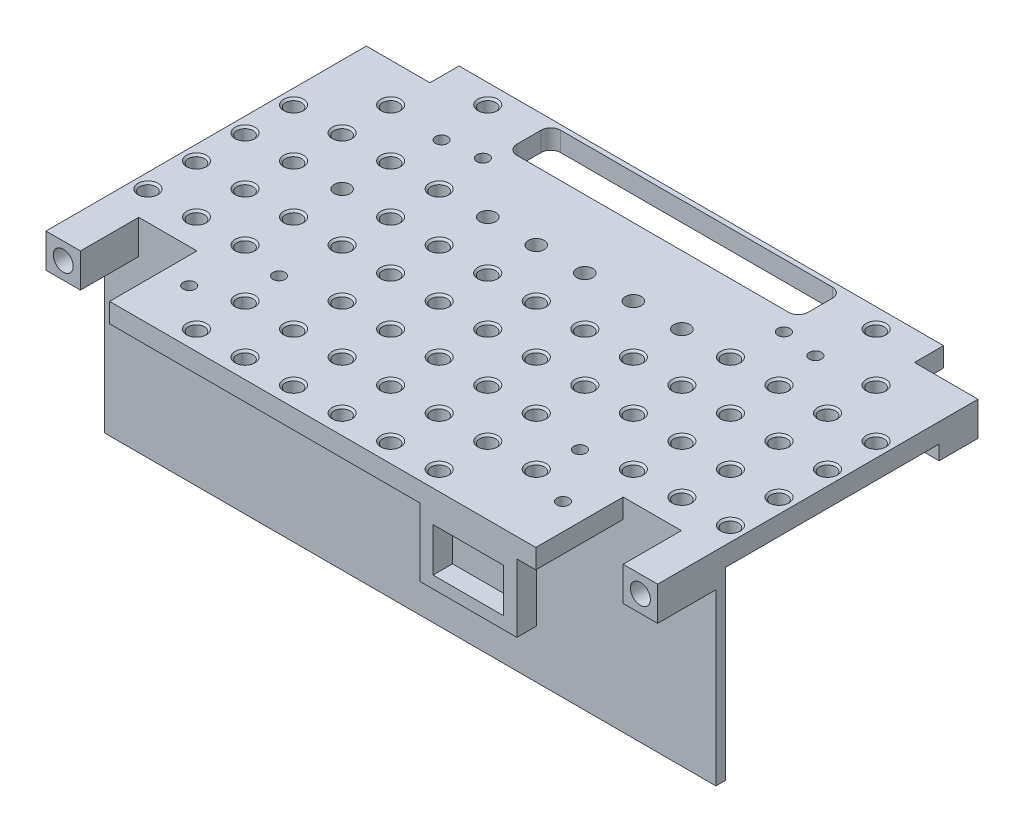
SolidWorks part; units mm, degrees
ref_plane "Front Plane" through (0, 0, 0) normal (0, 0, 1) x (1, 0, 0)
ref_plane "Top Plane" through (0, 0, 0) normal (0, 1, 0) x (1, 0, 0)
ref_plane "Right Plane" through (0, 0, 0) normal (1, 0, 0) x (0, 0, -1)
sketch "Sketch1" plane through (0, 0, 0) normal (0, 1, 0) x (1, 0, 0)
  line L0 (-63, 0) -> (63, 0) construction
  line L1 (-63, -33) -> (-55.9, -33)
  line L2 (-63, -33) -> (-63, 33)
  line L3 (-63, 33) -> (-55.9, 33)
  line L4 (63, -33) -> (63, 33)
  line L5 (-63, -33) -> (63, 33) construction
  line L6 (-63, 33) -> (63, -33) construction
  line L8 (-55.9, 33) -> (-55.9, 40)
  line L9 (-55.9, 40) -> (55.9, 40)
  line L10 (55.9, 33) -> (55.9, 40)
  line L11 (55.9, 33) -> (63, 33)
  line L12 (55.9, -33) -> (55.9, -40)
  line L13 (-55.9, -40) -> (55.9, -40)
  line L14 (-55.9, -33) -> (-55.9, -40)
  line L15 (55.9, -33) -> (63, -33)
  point P0 (0, 0)
  point P10 (0, 40)
  dimension "D1" = 126
  dimension "D2" = 66
  dimension "D3" = 7.1
  dimension "D4" = 7
extrude "Boss-Extrude1" add sketch "Sketch1" along normal blind 4
sketch "Sketch3" plane through (0, 0, 0) normal (0, -1, 0) x (1, 0, 0)
  line L0 (-63, -33) -> (-63, 33) construction
  line L1 (-55.9, -33) -> (-63, -33)
  line L2 (-55.9, -33) -> (-55.9, -25)
  line L3 (-55.9, -25) -> (-63, -25)
  line L4 (-63, -33) -> (-63, -25)
  dimension "D1" = 8
extrude "Boss-Extrude3" add sketch "Sketch3" along normal blind 3
sketch "Sketch4" plane through (0, 0, -33) normal (0, 0, -1) x (-1, 0, 0)
  line L0 (63, -3) -> (55.9, 4) construction
  circle A0 centre (59.45, 0.5) radius 2.05
  dimension "D1" = 4.1
extrude "Cut-Extrude1" cut sketch "Sketch4" against normal blind 7
mirror "Mirror1" about plane through (0, 0, 0) normal (1, 0, 0) of "Cut-Extrude1", "Boss-Extrude3"
mirror "Mirror2" about plane through (0, 0, 0) normal (0, 0, 1) of "Cut-Extrude1", "Boss-Extrude3", "Mirror1"
sketch "Sketch5" plane through (0, 4, 0) normal (0, 1, 0) x (1, 0, 0)
  line L0 (55.9, 40) -> (-55.9, 40) construction
  line L1 (-30, 38) -> (30, 38)
  line L2 (-30, 38) -> (-30, 29)
  line L3 (-30, 29) -> (30, 29)
  line L4 (30, 38) -> (30, 29)
  point P4 (0, 29)
  dimension "D1" = 2
  dimension "D2" = 9
  dimension "D3" = 60
extrude "Cut-Extrude2" cut sketch "Sketch5" against normal through all
sketch "Sketch6" plane through (0, 4, 0) normal (0, 1, 0) x (1, 0, 0)
  line L1 (-38.5, -28) -> (38.5, -28) construction
  line L2 (-38.5, -28) -> (-38.5, 24) construction
  line L3 (-38.5, 24) -> (38.5, 24) construction
  line L4 (38.5, -28) -> (38.5, 24) construction
  line L5 (-38.5, -28) -> (38.5, 24) construction
  line L6 (-38.5, 24) -> (38.5, -28) construction
  circle A0 centre (-38.5, 24) radius 1.25
  circle A1 centre (38.5, 24) radius 1.25
  circle A2 centre (38.5, -28) radius 1.25
  circle A3 centre (-38.5, -28) radius 1.25
  point P0 (0, -2)
  point P9 (0, -2)
  dimension "D4" = 2.5
  dimension "D1" = 77
  dimension "D2" = 52
  dimension "D3" = 2
fillet "Fillet1" radius 2 4 edges at (-30, 2, -38) (-30, 2, -29) (30, 2, -38) (30, 2, -29)
sketch "Sketch7" plane through (0, 4, 0) normal (0, 1, 0) x (1, 0, 0)
  line L0 (55.9, 33) -> (55.9, 40) construction
  line L1 (-55.9, 40) -> (55.9, 40)
  line L2 (-55.9, 40) -> (-55.9, 39)
  line L3 (-55.9, 39) -> (55.9, 39)
  line L4 (55.9, 40) -> (55.9, 39)
  line L5 (-55.9, -33) -> (-55.9, -40) construction
  line L6 (55.9, -40) -> (-55.9, -40)
  line L7 (55.9, -40) -> (55.9, -39)
  line L8 (55.9, -39) -> (-55.9, -39)
  line L9 (-55.9, -40) -> (-55.9, -39)
  dimension "D1" = 1
  dimension "D2" = 1
extrude "Cut-Extrude3" cut sketch "Sketch7" against normal through all
sketch "Sketch8" plane through (0, 0, 0) normal (0, -1, 0) x (1, 0, 0)
  line L0 (63, 25) -> (63, -25) construction
  line L1 (63, 21) -> (-63, 21)
  line L2 (63, 21) -> (63, 19)
  line L3 (63, 19) -> (-63, 19)
  line L4 (-63, 21) -> (-63, 19)
  line L5 (-63, -25) -> (-63, 25) construction
  line L7 (55.9, 39) -> (-55.9, 39) construction
  dimension "D1" = 20
  dimension "D2" = 2
extrude "Boss-Extrude4" add sketch "Sketch8" along normal blind 38
sketch "Sketch9" plane through (0, 4, 0) normal (0, 1, 0) x (1, 0, 0)
  line L0 (63, -21) -> (-63, -21) construction
  line L1 (-55.9, -39) -> (-43.9, -39)
  line L2 (-55.9, -39) -> (-55.9, -21)
  line L3 (-55.9, -21) -> (-43.9, -21)
  line L4 (-43.9, -39) -> (-43.9, -21)
  dimension "D1" = 12
extrude "Cut-Extrude4" cut sketch "Sketch9" against normal blind 10
sketch "Sketch10" plane through (0, -3, 0) normal (0, -1, 0) x (1, 0, 0)
  line L1 (-63, 25) -> (-55.9, 25)
  line L2 (-63, 25) -> (-63, 21)
  line L3 (-63, 21) -> (-55.9, 21)
  line L4 (-55.9, 25) -> (-55.9, 21)
  line L5 (55.9, 25) -> (63, 25)
  line L6 (55.9, 25) -> (55.9, 21)
  line L7 (55.9, 21) -> (63, 21)
  line L8 (63, 25) -> (63, 21)
extrude "Boss-Extrude5" add sketch "Sketch10" against normal up to surface (3 mm away) up to face at (29.4143, 0, 29)
ref_plane "Plane2" through (-56, 0, 0) normal (-1, 0, 0) x (0, 0, 1)
sketch "Sketch12" plane through (-56, 0, 0) normal (-1, 0, 0) x (0, 0, 1)
  line L0 (21, -5.8) -> (21, -16.2)
  line L1 (21, -38) -> (21, -3) construction
  line L2 (21, -16.2) -> (23.7, -13.5)
  line L3 (23.7, -13.5) -> (23.7, -8.5)
  line L4 (23.7, -8.5) -> (21, -5.8)
  line L5 (23.7, -11) -> (21, -11) construction
  line L6 (21, -3) -> (33, -3) construction
  line L7 (23.1, -9) -> (21.6, -9)
  line L8 (23.1, -9) -> (23.1, -13)
  line L9 (23.1, -13) -> (21.6, -13)
  line L10 (21.6, -9) -> (21.6, -13)
  line L11 (21, -20.8) -> (21, -31.2)
  line L12 (21, -31.2) -> (23.7, -28.5)
  line L13 (23.7, -28.5) -> (23.7, -23.5)
  line L14 (23.7, -23.5) -> (21, -20.8)
  line L15 (23.1, -24) -> (21.6, -24)
  line L16 (23.1, -24) -> (23.1, -28)
  line L17 (23.1, -28) -> (21.6, -28)
  line L18 (21.6, -24) -> (21.6, -28)
  line L19 (23.7, -26) -> (21, -26) construction
  point P13 (22.35, -11)
  point P14 (23.1, -11)
  dimension "D1" = 1.5
  dimension "D2" = 0.6
  dimension "D3" = 0.6
  dimension "D4" = 4
  dimension "D5" = 45
  dimension "D6" = 5
  dimension "D7" = 8
  dimension "D8" = 2
extrude "Boss-Extrude6" add sketch "Sketch12" against normal blind 2
ref_plane "Plane3" through (-49.9, 0, 0) normal (1, 0, 0) x (0, 0, -1)
mirror "Mirror3" about plane through (-49.9, 0, 0) normal (1, 0, 0) of "Boss-Extrude6"
sketch "Sketch13" plane through (0, 0, 0) normal (0, -1, 0) x (1, 0, 0)
  line L0 (-28, -29) -> (28, -29) construction
  line L1 (-20, -19.5) -> (20, -19.5)
  line L2 (-20, -19.5) -> (-20, -21.5)
  line L3 (-20, -21.5) -> (20, -21.5)
  line L4 (20, -19.5) -> (20, -21.5)
  point P4 (0, -21.5)
  dimension "D1" = 40
  dimension "D2" = 2
  dimension "D3" = 7.5
extrude "Boss-Extrude7" add sketch "Sketch13" along normal up to surface (38 mm away) up to face at (0, -38, 20)
sketch "Sketch14" plane through (0, 0, 0) normal (1, 0, 0) x (0, 0, -1)
  line L0 (-19, -19) -> (19.5, -19) construction
  line L1 (-19, -38) -> (-19, 0) construction
  line L2 (19.5, -38) -> (19.5, 0) construction
  line L3 (0.25, -38) -> (0.25, 0) construction
  line L4 (-19, 0) -> (25, 0) construction
  line L5 (-21, -31.2) -> (-23.7, -28.5) construction
  line L6 (-23.1, -24) -> (-21.6, -24) construction
  line L7 (-23.1, -28) -> (-23.1, -24) construction
  line L8 (-21.6, -28) -> (-23.1, -28) construction
  line L9 (-21.6, -24) -> (-21.6, -28) construction
  line L10 (-21, -20.8) -> (-21, -31.2) construction
  line L11 (-23.7, -23.5) -> (-21, -20.8) construction
  line L12 (-23.7, -28.5) -> (-23.7, -23.5) construction
  line L13 (-23.1, -13) -> (-23.1, -9) construction
  line L14 (-23.1, -9) -> (-21.6, -9) construction
  line L15 (-21.6, -9) -> (-21.6, -13) construction
  line L16 (-21.6, -13) -> (-23.1, -13) construction
  line L17 (-21, -5.8) -> (-21, -16.2) construction
  line L18 (-21, -16.2) -> (-23.7, -13.5) construction
  line L19 (-23.7, -13.5) -> (-23.7, -8.5) construction
  line L20 (-23.7, -8.5) -> (-21, -5.8) construction
  line L21 (-21, -31.2) -> (-23.7, -28.5) construction
  line L22 (-23.1, -24) -> (-21.6, -24) construction
  line L23 (-23.1, -28) -> (-23.1, -24) construction
  line L24 (-21.6, -28) -> (-23.1, -28) construction
  line L25 (-21.6, -24) -> (-21.6, -28) construction
  line L26 (-21, -20.8) -> (-21, -31.2) construction
  line L27 (-23.7, -23.5) -> (-21, -20.8) construction
  line L28 (-23.7, -28.5) -> (-23.7, -23.5) construction
  line L29 (-23.1, -13) -> (-23.1, -9) construction
  line L30 (-23.1, -9) -> (-21.6, -9) construction
  line L31 (-21.6, -9) -> (-21.6, -13) construction
  line L32 (-21.6, -13) -> (-23.1, -13) construction
  line L33 (-21, -5.8) -> (-21, -16.2) construction
  line L34 (-21, -16.2) -> (-23.7, -13.5) construction
  line L35 (-23.7, -13.5) -> (-23.7, -8.5) construction
  line L36 (-23.7, -8.5) -> (-21, -5.8) construction
  line L37 (24.2, -8.5) -> (21.5, -5.8)
  line L38 (24.2, -13.5) -> (24.2, -8.5)
  line L39 (21.5, -16.2) -> (24.2, -13.5)
  line L40 (21.5, -5.8) -> (21.5, -16.2)
  line L41 (22.1, -13) -> (23.6, -13)
  line L42 (22.1, -9) -> (22.1, -13)
  line L43 (23.6, -9) -> (22.1, -9)
  line L44 (23.6, -13) -> (23.6, -9)
  line L45 (24.2, -28.5) -> (24.2, -23.5)
  line L46 (24.2, -23.5) -> (21.5, -20.8)
  line L47 (21.5, -20.8) -> (21.5, -31.2)
  line L48 (22.1, -24) -> (22.1, -28)
  line L49 (22.1, -28) -> (23.6, -28)
  line L50 (23.6, -28) -> (23.6, -24)
  line L51 (23.6, -24) -> (22.1, -24)
  line L52 (21.5, -31.2) -> (24.2, -28.5)
  point P11 (0.25, -19)
extrude "Boss-Extrude8" add sketch "Sketch14" along normal mid plane 2
sketch "Sketch15" plane through (0, 0, 0) normal (1, 0, 0) x (0, 0, -1)
  line L0 (19.5, 0) -> (19.5, -5)
  line L1 (19.5, -38) -> (19.5, 0) construction
  line L2 (19.5, -5) -> (16.6132, 0)
  line L3 (-19, 0) -> (25, 0) construction
  line L4 (16.6132, 0) -> (19.5, 0)
  dimension "D1" = 60
  dimension "D2" = 5
extrude "Boss-Extrude9" add sketch "Sketch15" against normal up to surface and the other way up to surface up to face at (-20, -19, -20.5) other way up to face at (20, -19, -20.5)
sketch "Sketch16" plane through (0, 0, 39) normal (0, 0, 1) x (1, 0, 0)
  line L0 (40, 0) -> (20, -14) construction
  line L1 (40, 0) -> (20, 0)
  line L2 (40, 0) -> (40, -14)
  line L3 (40, -14) -> (20, -14)
  line L4 (20, 0) -> (20, -14)
  line L5 (55.9, 0) -> (-43.9, 0) construction
  line L6 (22.75, -2.5) -> (37.25, -2.5)
  line L7 (22.75, -2.5) -> (22.75, -11.5)
  line L8 (22.75, -11.5) -> (37.25, -11.5)
  line L9 (37.25, -2.5) -> (37.25, -11.5)
  line L10 (22.75, -2.5) -> (37.25, -11.5) construction
  line L11 (22.75, -11.5) -> (37.25, -2.5) construction
  line L12 (63, -38) -> (63, -3) construction
  point P5 (30, -7)
  dimension "D1" = 20
  dimension "D2" = 14
  dimension "D3" = 14.5
  dimension "D4" = 9
  dimension "D5" = 23
extrude "Boss-Extrude10" add sketch "Sketch16" against normal blind 4
sketch "Sketch17" plane through (0, 0, 0) normal (0, -1, 0) x (1, 0, 0)
  line L6 (-43.9, 21) -> (-55.9, 21) construction
  line L7 (55.9, 39) -> (43.9, 39)
  line L8 (55.9, 39) -> (55.9, 21)
  line L9 (55.9, 21) -> (43.9, 21)
  line L10 (43.9, 39) -> (43.9, 21)
  line L13 (-43.9, 39) -> (-43.9, 21) construction
extrude "Cut-Extrude5" cut sketch "Sketch17" against normal through all
sketch "Sketch18" plane through (0, 4, 0) normal (0, 1, 0) x (1, 0, 0)
  line L5 (-55.9, 39) -> (55.9, 39) construction
  line L6 (55.9, 33) -> (49.9, 33)
  line L7 (55.9, 33) -> (55.9, 39)
  line L8 (55.9, 39) -> (49.9, 39)
  line L9 (49.9, 33) -> (49.9, 39)
  line L11 (-55.9, 33) -> (-49.9, 33)
  line L12 (-55.9, 33) -> (-55.9, 39)
  line L13 (-55.9, 39) -> (-49.9, 39)
  line L14 (-49.9, 33) -> (-49.9, 39)
extrude "Cut-Extrude6" cut sketch "Sketch18" against normal through all
sketch "Sketch20" plane through (0, 4, 0) normal (0, 1, 0) x (1, 0, 0)
  line L0 (-31, 25) -> (31, -17) construction
  line L1 (-31, 25) -> (31, 25) construction
  line L2 (-31, 25) -> (-31, -17) construction
  line L3 (-31, -17) -> (31, -17) construction
  line L4 (31, 25) -> (31, -17) construction
  line L5 (-38.5, 26) -> (38.5, 26) construction
  line L6 (-38.5, 26) -> (-38.5, -26) construction
  line L7 (-38.5, -26) -> (38.5, -26) construction
  line L8 (38.5, 26) -> (38.5, -26) construction
  line L11 (38.5, 26) -> (-38.5, -26) construction
  circle A0 centre (-31, 25) radius 3 construction
  circle A1 centre (-31, -17) radius 3 construction
  circle A2 centre (31, -17) radius 3 construction
  circle A3 centre (31, 25) radius 3 construction
  circle A4 centre (-38.5, 26) radius 3 construction
  circle A5 centre (38.5, 26) radius 3 construction
  circle A6 centre (38.5, -26) radius 3 construction
  circle A7 centre (-38.5, -26) radius 3 construction
  point P18 (0, 4)
  dimension "D3" = 6
  dimension "D1" = 42
  dimension "D2" = 62
  dimension "D4" = 4
  dimension "D6" = 77
  dimension "D7" = 52
sketch "Sketch22" plane through (0, 4, 0) normal (0, 1, 0) x (1, 0, 0)
  circle A0 centre (-31, 25) radius 1.25
  circle A1 centre (31, 25) radius 1.25
  circle A2 centre (31, -17) radius 1.25
  circle A3 centre (-31, -17) radius 1.25
  dimension "D1" = 2.5
extrude "Cut-Extrude7" cut sketch "Sketch22" against normal up to surface (4 mm away) up to face at (15, 0, 33.5)
sketch "Sketch23" plane through (0, 4, 0) normal (0, 1, 0) x (1, 0, 0)
  line L0 (-63, 0) -> (63, 0) construction
  line L1 (63, -33) -> (63, 33) construction
  line L2 (0, -39) -> (0, 39) construction
  line L3 (-49.9, 39) -> (49.9, 39) construction
  line L4 (-63, -5) -> (63, -5) construction
  line L5 (-63, -15) -> (63, -15) construction
  line L9 (-10, -5) -> (-10, -15) construction
  line L10 (-20, -5) -> (-20, -15) construction
  line L11 (-30, -5) -> (-30, -15) construction
  line L12 (-40, -5) -> (-40, -15) construction
  line L13 (-50, -5) -> (-50, -15) construction
  line L14 (-60, -5) -> (-60, -15) construction
  circle A0 centre (0, -5) radius 1.65
  circle A1 centre (0, -15) radius 1.65
  circle A2 centre (-10, -5) radius 1.65
  circle A3 centre (-20, -5) radius 1.65
  circle A4 centre (-30, -5) radius 1.65
  circle A5 centre (-40, -5) radius 1.65
  circle A6 centre (-50, -5) radius 1.65
  circle A7 centre (-60, -5) radius 1.65
  circle A8 centre (-60, -15) radius 1.65
  circle A9 centre (-50, -15) radius 1.65
  circle A10 centre (-40, -15) radius 1.65
  circle A11 centre (-20, -15) radius 1.65
  circle A12 centre (-10, -15) radius 1.65
  point P6 (0, 0)
  point P11 (0, 0)
  point P18 (0, -5)
  point P21 (0, -15)
  dimension "D1" = 3.3
  dimension "D4" = 10
  dimension "D2" = 5
  dimension "D3" = 10
  dimension "D5" = 10
  dimension "D6" = 10
  dimension "D7" = 10
  dimension "D8" = 10
  dimension "D9" = 10
extrude "Cut-Extrude8" cut sketch "Sketch23" against normal through all
mirror "Mirror4" about plane through (0, 0, 0) normal (0, 0, 1) of "Cut-Extrude8"
mirror "Mirror5" about plane through (0, 0, 0) normal (1, 0, 0) of "Mirror4", "Cut-Extrude8"
sketch "Sketch24" plane through (0, 4, 0) normal (0, 1, 0) x (1, 0, 0)
  line L0 (-40, 15) -> (-20, 15) construction
  line L1 (20, 15) -> (40, 15) construction
  line L2 (-40, 15) -> (-40, 39) construction
  line L3 (-49.9, 39) -> (49.9, 39) construction
  line L4 (-50, 15) -> (-50, 33) construction
  line L5 (-49.9, 33) -> (-63, 33) construction
  line L6 (-50, 25) -> (-40, 25) construction
  line L7 (-50, 35) -> (-40, 35) construction
  line L8 (40, 15) -> (40, 39) construction
  line L9 (50, 15) -> (50, 33) construction
  line L10 (63, 33) -> (49.9, 33) construction
  line L11 (40, 25) -> (50, 25) construction
  line L12 (50, 35) -> (40, 35) construction
  line L13 (-30, -5) -> (-30, -39) construction
  line L14 (43.9, -39) -> (-43.9, -39) construction
  line L16 (30, -5) -> (30, -39) construction
  line L17 (-20, -5) -> (-20, -39) construction
  line L18 (-10, -5) -> (-10, -39) construction
  line L19 (0, -5) -> (0, -39) construction
  line L20 (10, -5) -> (10, -39) construction
  line L21 (20, -5) -> (20, -39) construction
  line L22 (-30, -25) -> (30, -25) construction
  line L23 (-30, -35) -> (30, -35) construction
  circle A0 centre (-30, 15) radius 1.65
  circle A1 centre (30, 15) radius 1.65
  circle A2 centre (-40, 15) radius 1.65 construction
  circle A3 centre (-40, 35) radius 1.65
  circle A4 centre (-40, 25) radius 1.65 construction
  circle A5 centre (-50, 25) radius 1.65
  circle A6 centre (40, 25) radius 1.65 construction
  circle A7 centre (50, 25) radius 1.65
  circle A8 centre (40, 35) radius 1.65
  circle A9 centre (-10, 15) radius 1.65 construction
  circle A10 centre (-20, -15) radius 1.65 construction
  circle A11 centre (30, -25) radius 1.65
  circle A13 centre (-30, -25) radius 1.65
  circle A14 centre (-30, -35) radius 1.65
  circle A15 centre (-10, -25) radius 1.65
  circle A16 centre (-10, -35) radius 1.65
  circle A17 centre (0, -25) radius 1.65
  circle A18 centre (0, -35) radius 1.65
  circle A19 centre (10, -25) radius 1.65
  circle A20 centre (10, -35) radius 1.65
  circle A21 centre (20, -35) radius 1.65
  circle A22 centre (20, -25) radius 1.65
  circle A23 centre (-20, -25) radius 1.65
  circle A24 centre (-20, -35) radius 1.65
  circle A26 centre (20, -15) radius 1.65 construction
  dimension "D1" = 10
  dimension "D2" = 10
  dimension "D3" = 10
  dimension "D4" = 10
  dimension "D5" = 10
  dimension "D6" = 10
extrude "Cut-Extrude9" cut sketch "Sketch24" against normal through all
chamfer "Chamfer1" distance 0.4 angle 45 121 edges at (-60, 0, 6.65) (-60, 4, 6.65) (-60, 0, -13.35) (-60, 4, -16.65) (-60, 0, -3.35) (-60, 4, -6.65) (-50, 0, -23.35) (-50, 4, -23.35) (-50, 0, -13.35) (-50, 4, -16.65) (-50, 0, -3.35) (-50, 4, -6.65) (-50, 0, 6.65) (-50, 4, 6.65) (-60, 0, 16.65) (-60, 4, 16.65) (-50, 0, 16.65) (-50, 4, 16.65) (-40, 0, 16.65) (-40, 4, 16.65) (-40, 0, 6.65) (-40, 4, 6.65) (-40, 0, -33.35) (-40, 4, -33.35) (-40, 0, -13.35) (-40, 4, -16.65) (-30, 0, -13.35) (-30, 4, -13.35) (-30, 0, -3.35) (-30, 4, -6.65) (-20, 0, 6.65) (-20, 4, 6.65) (-10, 0, 16.65) (-10, 4, 16.65) (60, 0, 16.65) (60, 4, 16.65) (60, 0, 6.65) (60, 4, 6.65) (60, 0, -3.35) (60, 4, -6.65) (60, 0, -13.35) (60, 4, -16.65) (50, 0, -23.35) (50, 4, -23.35) (40, 0, -13.35) (40, 4, -16.65) (40, 0, -33.35) (40, 4, -33.35) (50, 0, -13.35) (50, 4, -16.65) (50, 0, -3.35) (50, 4, -6.65) (50, 0, 16.65) (50, 4, 16.65) (50, 0, 6.65) (50, 4, 6.65) (40, 0, 6.65) (40, 4, 6.65) (40, 0, 16.65) (40, 4, 16.65) (40, 0, -3.35) (40, 4, -6.65) (30, 0, -3.35) (30, 4, -6.65) (30, 0, -13.35) (30, 4, -13.35) (20, 0, -3.35) (20, 4, -6.65) (30, 0, 6.65) (30, 4, 6.65) (20, 0, 6.65) (20, 4, 6.65) (20, 0, 16.65) (20, 4, 16.65) (30, 0, 26.65) (30, 4, 26.65) (20, 0, 26.65) (20, 4, 26.65) (10, 0, 36.65) (10, 4, 36.65) (10, 0, 26.65) (10, 4, 26.65) (10, 0, 16.65) (10, 4, 16.65) (10, 0, 6.65) (10, 4, 6.65) (10, 0, -3.35) (10, 4, -6.65) (0, 0, -3.35) (0, 4, -6.65) (0, 0, 6.65) (0, 4, 6.65) (0, 0, 16.65) (0, 4, 16.65) (0, 0, 26.65) (0, 4, 26.65) (0, 0, 36.65) (0, 4, 36.65) (-10, 0, 36.65) (-10, 4, 36.65) (-10, 0, 26.65) (-10, 4, 26.65) (-10, 0, 6.65) (-10, 4, 6.65) (-10, 0, -3.35) (-10, 4, -6.65) (-20, 0, -3.35) (-20, 4, -6.65) (-20, 0, 16.65) (-20, 4, 16.65) (-20, 0, 26.65) (-20, 4, 26.65) (-20, 0, 36.65) (-20, 4, 36.65) (-30, 0, 36.65) (-30, 4, 36.65) (-30, 0, 26.65) (-30, 4, 26.65) (-30, 0, 6.65) (-30, 4, 6.65) (20, 4, 36.65)
extrude "Cut-Extrude10" cut sketch "Sketch6" against normal up to surface (4 mm away) up to face at (30, 0, 27.05)
sketch "Sketch25" plane through (0, 0, -21.5) normal (0, 0, -1) x (-1, 0, 0)
  line L0 (63, -38) -> (-63, -38) construction
  line L1 (-20, -38) -> (-14, -38)
  line L2 (-20, -38) -> (-20, 0)
  line L3 (-20, 0) -> (-14, 0)
  line L4 (-14, -38) -> (-14, 0)
  line L5 (-20, -38) -> (-20, 0) construction
  line L6 (20, 0) -> (-20, 0) construction
  line L7 (-20, -38) -> (20, -38) construction
  line L8 (20, 0) -> (14, 0)
  line L9 (20, 0) -> (20, -38)
  line L10 (20, -38) -> (14, -38)
  line L11 (14, 0) -> (14, -38)
  dimension "D1" = 6
extrude "Cut-Extrude11" cut sketch "Sketch25" against normal blind 10
sketch "Sketch26" plane through (-1, 0, 0) normal (-1, 0, 0) x (0, 0, 1)
  line L1 (-21.5, -5.8) -> (-27.2016, -5.8)
  line L2 (-21.5, -5.8) -> (-21.5, -36.3625)
  line L3 (-21.5, -36.3625) -> (-27.2016, -36.3625)
  line L4 (-27.2016, -5.8) -> (-27.2016, -36.3625)
  line L5 (21, -5.8) -> (28.5342, -5.8)
  line L6 (21, -5.8) -> (21, -34.3243)
  line L7 (21, -34.3243) -> (28.5342, -34.3243)
  line L8 (28.5342, -5.8) -> (28.5342, -34.3243)
extrude "Cut-Extrude12" cut sketch "Sketch26" against normal through all both and the other way through all
